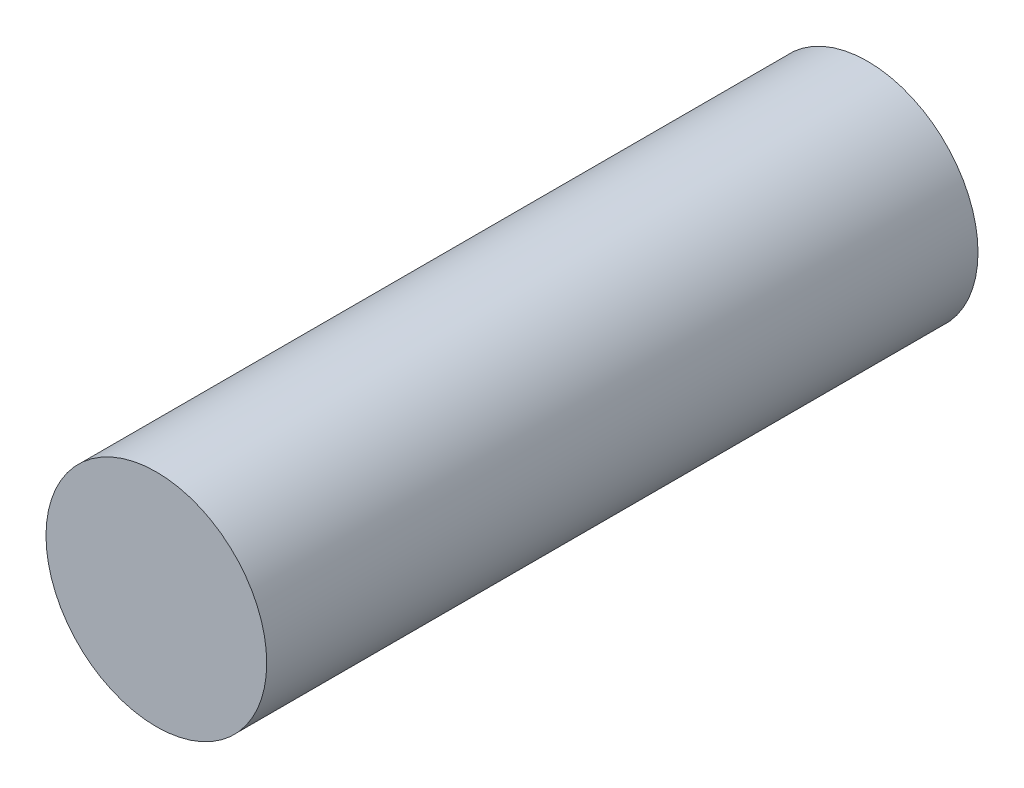
SolidWorks part; units mm, degrees
ref_plane "前视基准面" through (0, 0, 0) normal (0, 0, 1) x (1, 0, 0)
ref_plane "上视基准面" through (0, 0, 0) normal (0, 1, 0) x (1, 0, 0)
ref_plane "右视基准面" through (0, 0, 0) normal (1, 0, 0) x (0, 0, -1)
sketch "草图1" plane through (0, 0, 0) normal (0, 0, 1) x (1, 0, 0)
  circle A0 centre (-0.0227, -0.0064) radius 2.5
extrude "凸台-拉伸1" add sketch "草图1" along normal blind 16.1127
